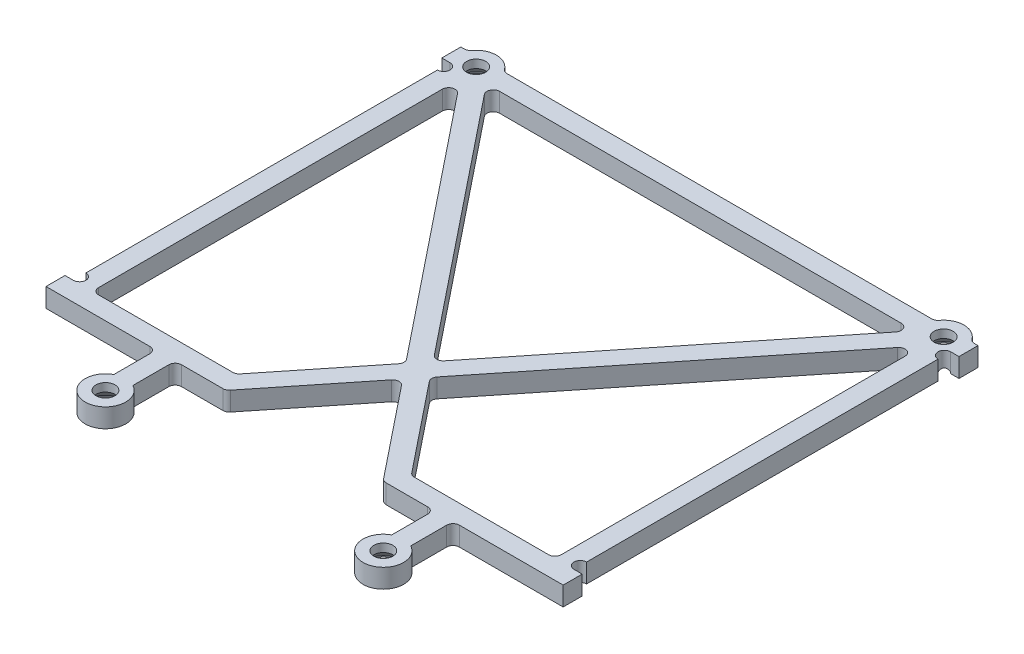
SolidWorks part; units mm, degrees
ref_plane "Front Plane" through (0, 0, 0) normal (0, 0, 1) x (1, 0, 0)
ref_plane "Top Plane" through (0, 0, 0) normal (0, 1, 0) x (1, 0, 0)
ref_plane "Right Plane" through (0, 0, 0) normal (1, 0, 0) x (0, 0, -1)
sketch "Sketch1" plane through (0, 0, 0) normal (0, 1, 0) x (1, 0, 0)
  line L0 (-36.88, 36.725) -> (36.88, 36.725) construction
  line L1 (-39.5, -24.225) -> (-39.5, 35.225)
  line L2 (21.92, -36.725) -> (-21.92, -36.725) construction
  line L3 (-36.5, -24.225) -> (-36.5, 35.225)
  line L4 (0, -40.095) -> (0, -36.725) construction
  line L5 (0, 36.725) -> (0, -36.725) construction
  line L6 (40.8, 38.225) -> (-40.8, 38.225)
  line L9 (40.8, 38.225) -> (40.8, 35.225)
  line L17 (40.8, 35.225) -> (-40.8, 35.225)
  line L18 (-40.8, 38.225) -> (-40.8, 35.225)
  line L23 (40.8, 38.225) -> (-40.8, 35.225) construction
  line L24 (40.8, 35.225) -> (-40.8, 38.225) construction
  line L60 (-21.92, -36.725) -> (36.88, 36.725) construction
  line L62 (21.92, -36.725) -> (-36.88, 36.725) construction
  line L66 (23.091, -35.7876) -> (-35.709, 37.6624)
  line L67 (20.749, -37.6624) -> (-38.051, 35.7876)
  line L68 (-20.749, -37.6624) -> (38.051, 35.7876)
  line L69 (-23.091, -35.7876) -> (35.709, 37.6624)
  line L71 (-36.5, 5.5) -> (-39.5, 5.5) construction
  line L73 (36.5, -24.225) -> (36.5, 35.225)
  line L74 (39.5, -24.225) -> (39.5, 35.225)
  line L75 (-36.5, -24.225) -> (-36.5, -27.225) construction
  line L76 (-40.8, -24.225) -> (40.8, -24.225)
  line L77 (-40.8, -24.225) -> (-40.8, -27.225)
  line L78 (-40.8, -27.225) -> (40.8, -27.225)
  line L79 (40.8, -24.225) -> (40.8, -27.225)
  line L80 (-40.8, -24.225) -> (40.8, -27.225) construction
  line L81 (-40.8, -27.225) -> (40.8, -24.225) construction
  line L82 (-21.92, -36.725) -> (-21.92, -27.225) construction
  line L84 (-23.42, -27.225) -> (-20.42, -27.225)
  line L85 (-23.42, -27.225) -> (-23.42, -33.8983)
  line L86 (-23.42, -33.8983) -> (-20.42, -33.8983)
  line L87 (-20.42, -27.225) -> (-20.42, -33.8983)
  line L88 (-23.42, -27.225) -> (-20.42, -33.8983) construction
  line L89 (-23.42, -33.8983) -> (-20.42, -27.225) construction
  line L90 (20.42, -27.225) -> (20.42, -33.8983)
  line L91 (23.42, -27.225) -> (23.42, -33.8983)
  circle A0 centre (21.92, -36.725) radius 1.5
  circle A1 centre (-21.92, -36.725) radius 1.5
  circle A2 centre (-36.88, 36.725) radius 1.5
  circle A3 centre (36.88, 36.725) radius 1.5
  circle A4 centre (-36.88, 36.725) radius 3.2
  circle A5 centre (-21.92, -36.725) radius 3.2
  circle A6 centre (21.92, -36.725) radius 3.2
  circle A7 centre (36.88, 36.725) radius 3.2
  circle A8 centre (0, -40.095) radius 16
  circle A9 centre (-39.5, 34.225) radius 1
  circle A10 centre (39.5, 34.225) radius 1
  circle A11 centre (-39.5, -23.225) radius 1
  circle A12 centre (39.5, -23.225) radius 1
  point P10 (0, 0)
  point P18 (-21.92, -30.5617)
  point P58 (0, -25.725)
  dimension "D4" = 3
  dimension "D5" = 6.4
  dimension "D6" = 32
  dimension "D9" = 3
  dimension "D17" = 2
  dimension "D1" = 74.958
  dimension "D2" = 43.84
  dimension "D3" = 73.76
  dimension "D7" = 3.37
  dimension "D8" = 81.6
  dimension "D10" = 79
  dimension "D13" = 1.5
  dimension "D14" = 1.5
  dimension "D15" = 1.5
  dimension "D16" = 1.5
  dimension "D18" = 11
extrude "Shape" add sketch "Sketch1" along normal blind 3
fillet "Mill fillets" radius 1 22 edges at (34.0533, 1.5, -38.225) (39.7067, 1.5, -38.225) (-39.7067, 1.5, -38.225) (-34.0533, 1.5, -38.225) (1.9214, 1.5, 9.3436) (-1.9214, 1.5, 9.3436) (33.7577, 1.5, -35.225) (-33.7577, 1.5, -35.225) (0, 1.5, 11.7438) (-36.5, 1.5, 24.225) (13.8346, 1.5, 24.225) (36.5, 1.5, 24.225) (-13.8346, 1.5, 24.225) (36.5, 1.5, -33.8501) (-36.5, 1.5, -33.8501) (0, 1.5, 6.9435) (-23.42, 1.5, 27.225) (20.42, 1.5, 27.225) (23.42, 1.5, 27.225) (-20.42, 1.5, 27.225) (12.3934, 1.5, 27.225) (-12.3934, 1.5, 27.225)
hole_wizard "M3 countersunks" positions "Sketch2" profile "Sketch3" countersink size "M3" standard "ANSI Metric" end condition through all
sketch "Sketch2" plane through (0, 0, 0) normal (0, -1, 0) x (-1, 0, 0)
  point P0 (21.92, -36.725)
  point P3 (-21.92, -36.725)
  point P6 (-36.88, 36.725)
  point P9 (36.88, 36.725)
sketch "Sketch3" plane through (-21.92, 0, 36.725) normal (1, 0, 0) x (0, 0, -1)
  line L0 (0, 0) -> (0, 3)
  line L1 (0, 3) -> (1.5, 3)
  line L2 (1.5, 3) -> (1.5, 1.7)
  line L3 (1.5, 1.7) -> (3, 0.2)
  line L4 (3, 0.2) -> (3, 0)
  line L6 (3, 0) -> (0, 0)
  line L7 (-1.5, 1.7) -> (-3, 0.2) construction
  line L11 (0, -6.35) -> (0, 107.95) construction
  dimension "Thru Hole Dia." = 3
  dimension "Thru Hole Depth" = 3
  dimension "C'Sink Dia." = 6
  dimension "C'Sink Angle" = 90
  dimension "Head Clearance" = 0.2
sketch "Coordinate system sketch" plane through (0, 0, 0) normal (0, -1, 0) x (1, 0, 0)
  line L0 (-36.88, -39.925) -> (-40.8, -39.925) construction
  line L1 (-40.8, -39.925) -> (-40.8, -38.225) construction
  arc A0 (-39.4514, -38.6298) -> (-34.3086, -38.6298) centre (-36.88, -36.725) ccw construction
